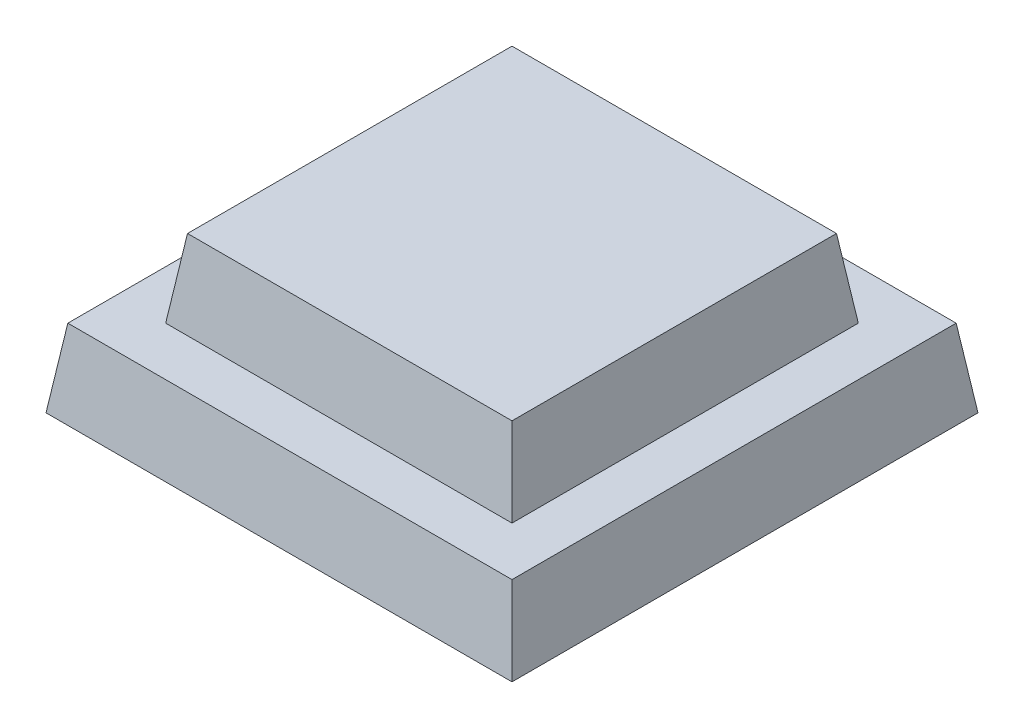
SolidWorks part; units mm, degrees
material "POLYURETHANE (11671)"
ref_plane "Front Plane" through (0, 0, 0) normal (0, 0, 1) x (1, 0, 0)
ref_plane "Top Plane" through (0, 0, 0) normal (0, 1, 0) x (1, 0, 0)
ref_plane "Right Plane" through (0, 0, 0) normal (1, 0, 0) x (0, 0, -1)
sketch "Sketch2" plane through (0, 0, 0) normal (0, 1, 0) x (1, 0, 0)
  line L1 (-9.525, 9.525) -> (9.525, 9.525)
  line L2 (-9.525, 9.525) -> (-9.525, -9.525)
  line L3 (-9.525, -9.525) -> (9.525, -9.525)
  line L4 (9.525, 9.525) -> (9.525, -9.525)
  line L5 (0, -9.525) -> (0, 9.525) construction
  line L6 (-9.525, 0) -> (9.525, 0) construction
  point P0 (0, 0)
  dimension "D1" = 19.05
  dimension "D2" = 19.05
extrude "Boss-Extrude1" add sketch "Sketch2" along normal blind 3.175 draft 8
sketch "Sketch3" plane through (0, 3.175, 0) normal (0, 1, 0) x (1, 0, 0)
  line L14 (-7.0788, -7.0788) -> (7.0788, -7.0788)
  line L15 (7.0788, -7.0788) -> (7.0788, 7.0788)
  line L16 (7.0788, 7.0788) -> (-7.0788, 7.0788)
  line L17 (-7.0788, 7.0788) -> (-7.0788, -7.0788)
  line L18 (-7.0788, -7.0788) -> (7.0788, -7.0788)
  line L19 (7.0788, -7.0788) -> (7.0788, 7.0788)
  line L20 (7.0788, 7.0788) -> (-7.0788, 7.0788)
  line L21 (-7.0788, 7.0788) -> (-7.0788, -7.0788)
  dimension "D1" = 2
extrude "Boss-Extrude2" add sketch "Sketch3" along normal blind 3.175 draft 8
